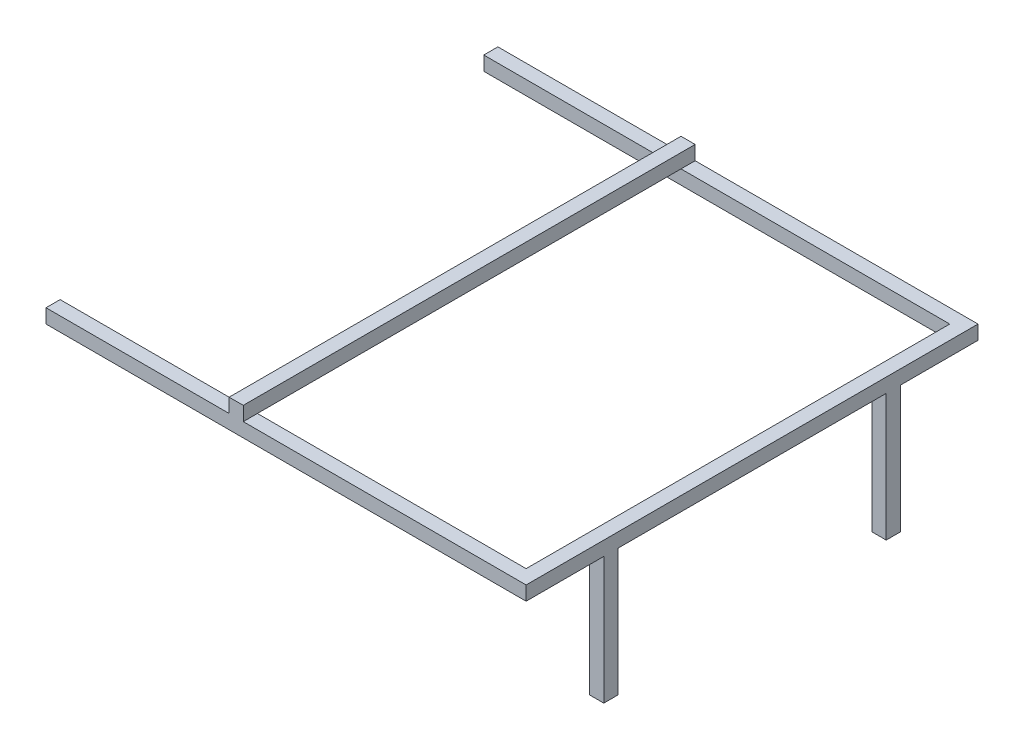
SolidWorks part; units mm, degrees
material "6061 合金"
ref_plane "前视基准面" through (0, 0, 0) normal (0, 0, 1) x (1, 0, 0)
ref_plane "上视基准面" through (0, 0, 0) normal (0, 1, 0) x (1, 0, 0)
ref_plane "右视基准面" through (0, 0, 0) normal (1, 0, 0) x (0, 0, -1)
sketch "草图1" plane through (0, 0, 0) normal (0, 1, 0) x (1, 0, 0)
  line L0 (-329.3879, -472.095) -> (-329.3879, -492.095)
  line L1 (-329.3879, 147.905) -> (350.6121, 147.905)
  line L2 (-329.3879, 147.905) -> (-329.3879, 127.905)
  line L3 (-329.3879, -492.095) -> (350.6121, -492.095)
  line L4 (350.6121, 147.905) -> (350.6121, -492.095)
  line L5 (-329.3879, 127.905) -> (-70.0006, 127.905)
  line L7 (-329.3879, -472.095) -> (-70.0006, -472.095)
  line L8 (330.6121, 127.905) -> (330.6121, -472.095)
  line L10 (-50.0006, 127.905) -> (-50.0006, -472.095)
  line L12 (-70.0006, 127.905) -> (-70.0006, -472.095)
  line L13 (-50.0006, -472.095) -> (330.6121, -472.095)
  line L14 (-50.0006, 127.905) -> (330.6121, 127.905)
  point P13 (-329.3879, 127.905)
  point P14 (-329.3879, -472.095)
  dimension "D1" = 680
  dimension "D2" = 640
  dimension "D3" = 20
  dimension "D5" = 20
  dimension "D6" = 20
  dimension "D7" = 20
extrude "凸台-拉伸1" add sketch "草图1" along normal blind 20
sketch "Sketch1" plane through (0, 20, 0) normal (0, 1, 0) x (1, 0, 0)
  line L0 (-50.0006, 127.905) -> (-50.0006, -472.095) construction
  line L1 (-70.0006, 127.905) -> (-70.0006, -472.095) construction
  line L2 (-50.0006, 147.905) -> (-50.0006, -492.095)
  line L3 (-70.0006, 147.905) -> (-70.0006, -492.095)
  line L4 (350.6121, 147.905) -> (-329.3879, 147.905) construction
  line L5 (-329.3879, -492.095) -> (350.6121, -492.095) construction
  line L6 (-70.0006, 147.905) -> (-50.0006, 147.905)
  line L7 (-70.0006, -492.095) -> (-50.0006, -492.095)
extrude "Boss-Extrude1" add sketch "Sketch1" along normal blind 20
sketch "Sketch2" plane through (0, 0, 0) normal (0, -1, 0) x (1, 0, 0)
  line L1 (-70.0006, 472.095) -> (-50.0006, 472.095)
  line L2 (-70.0006, 472.095) -> (-70.0006, -127.905)
  line L3 (-70.0006, -127.905) -> (-50.0006, -127.905)
  line L4 (-50.0006, 472.095) -> (-50.0006, -127.905)
extrude "Cut-Extrude1" cut sketch "Sketch2" against normal blind 20
sketch "Sketch3" plane through (0, 0, 0) normal (0, -1, 0) x (1, 0, 0)
  line L0 (350.6121, 492.095) -> (350.6121, -147.905) construction
  line L1 (350.6121, 382.095) -> (330.6121, 382.095)
  line L2 (350.6121, 382.095) -> (350.6121, 362.095)
  line L3 (350.6121, 362.095) -> (330.6121, 362.095)
  line L4 (330.6121, 382.095) -> (330.6121, 362.095)
  line L5 (330.6121, 472.095) -> (330.6121, -127.905) construction
  line L6 (300.6121, 492.095) -> (350.6121, 492.095) construction
  line L7 (350.6121, -147.905) -> (-329.3879, -147.905) construction
  line L8 (350.6121, -37.905) -> (330.6121, -37.905)
  line L9 (350.6121, -37.905) -> (350.6121, -17.905)
  line L10 (350.6121, -17.905) -> (330.6121, -17.905)
  line L11 (330.6121, -37.905) -> (330.6121, -17.905)
  dimension "D1" = 20
  dimension "D2" = 110
  dimension "D3" = 20
  dimension "D4" = 110
extrude "Boss-Extrude2" add sketch "Sketch3" along normal blind 180
